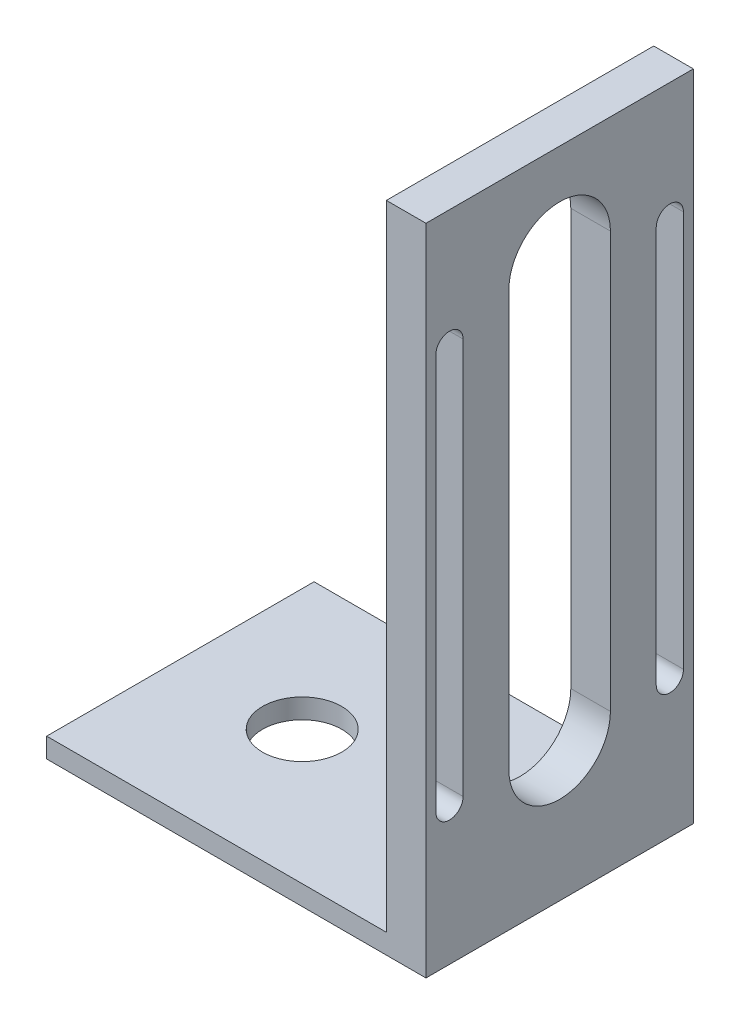
SolidWorks part; units mm, degrees
ref_plane "Front Plane" through (0, 0, 0) normal (0, 0, 1) x (1, 0, 0)
ref_plane "Top Plane" through (0, 0, 0) normal (0, 1, 0) x (1, 0, 0)
ref_plane "Right Plane" through (0, 0, 0) normal (1, 0, 0) x (0, 0, -1)
sketch "Sketch1" plane through (0, 0, 0) normal (0, 1, 0) x (1, 0, 0)
  line L0 (-55, 0) -> (55, 0) construction
  line L1 (-19.15, 13.5) -> (19.15, 13.5)
  line L2 (-19.15, 13.5) -> (-19.15, -13.5)
  line L3 (-19.15, -13.5) -> (19.15, -13.5)
  line L4 (19.15, 13.5) -> (19.15, -13.5)
  line L5 (-19.15, 13.5) -> (19.15, -13.5) construction
  line L6 (-19.15, -13.5) -> (19.15, 13.5) construction
  circle A0 centre (-6.85, 0) radius 4
  point P0 (0, 0)
  dimension "D3" = 8
  dimension "D1" = 27
  dimension "D2" = 38.3
  dimension "D4" = 26
extrude "Boss-Extrude1" add sketch "Sketch1" along normal blind 2
sketch "Sketch2" plane through (0, 2, 0) normal (0, 1, 0) x (1, 0, 0)
  line L0 (-19.15, -13.5) -> (19.15, -13.5) construction
  line L1 (19.15, 13.5) -> (15.15, 13.5)
  line L2 (19.15, 13.5) -> (19.15, -13.5)
  line L3 (19.15, -13.5) -> (15.15, -13.5)
  line L4 (15.15, 13.5) -> (15.15, -13.5)
  dimension "D1" = 4
extrude "Boss-Extrude2" add sketch "Sketch2" along normal blind 64
sketch "Sketch3" plane through (15.15, 0, 0) normal (-1, 0, 0) x (0, 0, 1)
  line L0 (-11.125, 14) -> (-11.125, 54) construction
  line L1 (-12.5, 14) -> (-12.5, 54)
  line L2 (-9.75, 14) -> (-9.75, 54)
  line L3 (-13.5, 66) -> (-13.5, 2) construction
  line L4 (-13.5, 66) -> (13.5, 66) construction
  line L5 (-13.5, 2) -> (13.5, 2) construction
  line L6 (0, -21.065) -> (0, 21.065) construction
  line L7 (11.125, 14) -> (11.125, 54) construction
  line L8 (12.5, 14) -> (12.5, 54)
  line L9 (9.75, 14) -> (9.75, 54)
  line L10 (0, 14) -> (0, 56) construction
  line L11 (-5.125, 14) -> (-5.125, 56)
  line L12 (5.125, 14) -> (5.125, 56)
  arc A0 (-12.5, 14) -> (-9.75, 14) centre (-11.125, 14) ccw
  arc A1 (-9.75, 54) -> (-12.5, 54) centre (-11.125, 54) ccw
  arc A2 (12.5, 14) -> (9.75, 14) centre (11.125, 14) cw
  arc A3 (9.75, 54) -> (12.5, 54) centre (11.125, 54) cw
  arc A4 (-5.125, 14) -> (5.125, 14) centre (0, 14) ccw
  arc A5 (5.125, 56) -> (-5.125, 56) centre (0, 56) ccw
  point P2 (-11.125, 34)
  point P17 (11.125, 34)
  point P25 (0, 35)
  dimension "D3" = 12
  dimension "D4" = 12
  dimension "D6" = 10
  dimension "D7" = 12
  dimension "D1" = 2.75
  dimension "D2" = 1
  dimension "D5" = 10.25
extrude "Cut-Extrude1" cut sketch "Sketch3" against normal up to next
